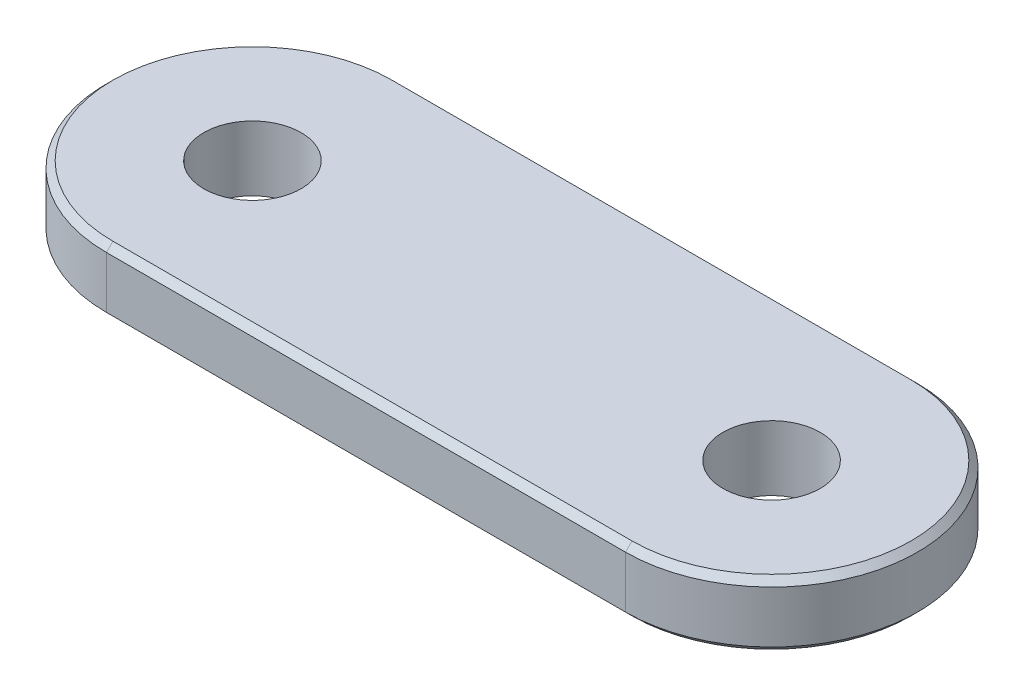
SolidWorks part; units mm, degrees
ref_plane "Front Plane" through (0, 0, 0) normal (0, 0, 1) x (1, 0, 0)
ref_plane "Top Plane" through (0, 0, 0) normal (0, 1, 0) x (1, 0, 0)
ref_plane "Right Plane" through (0, 0, 0) normal (1, 0, 0) x (0, 0, -1)
sketch "Sketch1" plane through (0, 0, 0) normal (0, 1, 0) x (1, 0, 0)
  line L0 (0, 45) -> (0, 129.9619) construction
  line L1 (-80, 45) -> (80, 45)
  line L2 (80, -45) -> (-80, -45)
  arc A0 (-80, 45) -> (-80, -45) centre (-80, 0) ccw
  arc A1 (80, 45) -> (80, -45) centre (80, 0) cw
  dimension "D1" = 90
  dimension "D2" = 80
extrude "Boss-Extrude1" add sketch "Sketch1" along normal blind 20
sketch "Sketch2" plane through (0, 20, 0) normal (0, 1, 0) x (1, 0, 0)
  line L0 (0, 0) -> (0, 74.8979) construction
  circle A0 centre (-80, 0) radius 15
  circle A1 centre (80, 0) radius 15
  dimension "D1" = 30
extrude "Cut-Extrude1" cut sketch "Sketch2" against normal through all
chamfer "Chamfer1" distance 2 angle 45 8 edges at (0, 20, -45) (-125, 20, 0) (125, 20, 0) (0, 20, 45) (0, 0, -45) (-125, 0, 0) (125, 0, 0) (0, 0, 45)
